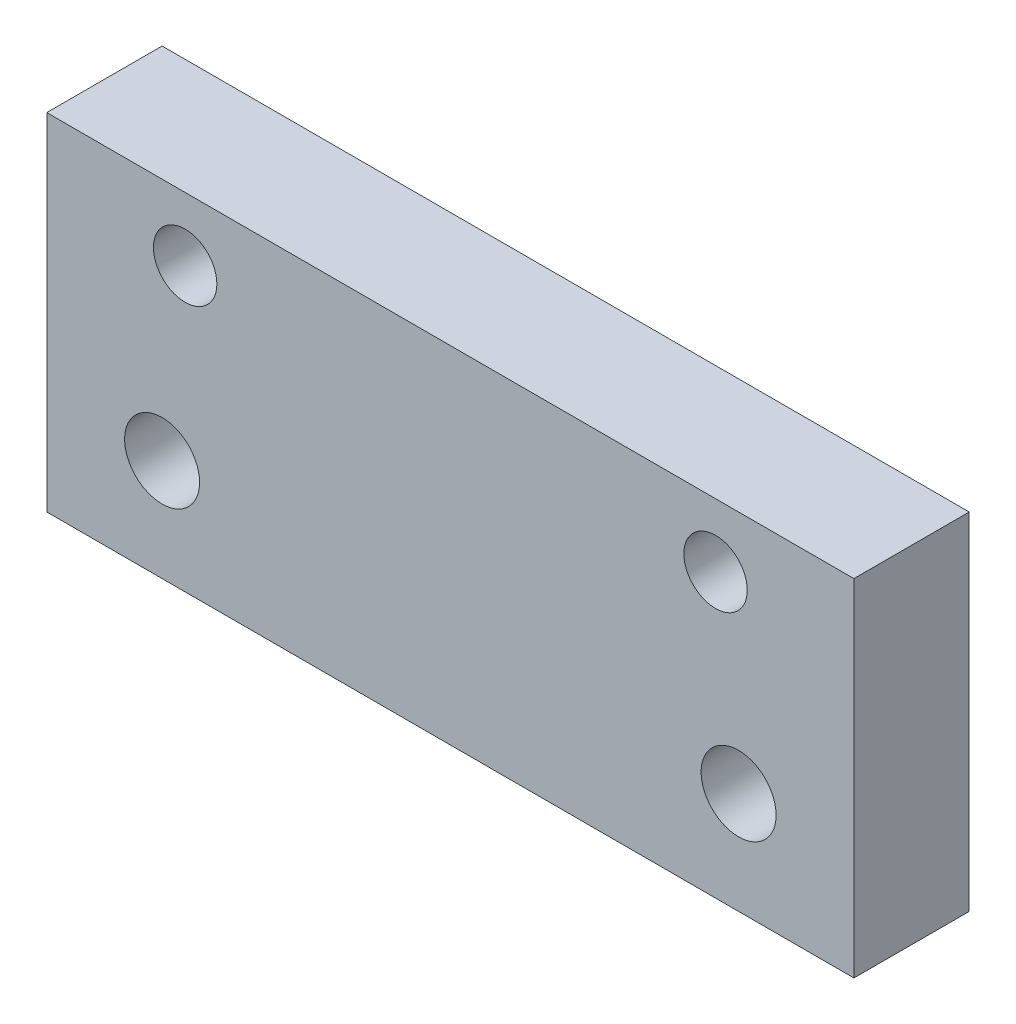
SolidWorks part; units mm, degrees
ref_plane "Front Plane" through (0, 0, 0) normal (0, 0, 1) x (1, 0, 0)
ref_plane "Top Plane" through (0, 0, 0) normal (0, 1, 0) x (1, 0, 0)
ref_plane "Right Plane" through (0, 0, 0) normal (1, 0, 0) x (0, 0, -1)
sketch "Sketch1" plane through (0, 0, 0) normal (0, 0, 1) x (1, 0, 0)
  line L1 (-35, 15) -> (35, 15)
  line L2 (-35, 15) -> (-35, -15)
  line L3 (-35, -15) -> (35, -15)
  line L4 (35, 15) -> (35, -15)
  line L5 (-35, 15) -> (35, -15) construction
  line L6 (-35, -15) -> (35, 15) construction
  circle A0 centre (-25, -6.1504) radius 3.25
  circle A1 centre (25, -6.1504) radius 3.25
  circle A2 centre (-23, 9.5) radius 2.75
  circle A3 centre (23, 9.5) radius 2.75
  point P0 (0, 0)
  point P14 (0, 0)
  point P15 (0, 0)
  point P17 (0, 0)
  dimension "D3" = 6.5
  dimension "D4" = 6.5
  dimension "D7" = 5.5
  dimension "D1" = 70
  dimension "D2" = 30
  dimension "D5" = 10
  dimension "D6" = 10
  dimension "D8" = 12
  dimension "D9" = 58
  dimension "D10" = 5.5
extrude "Boss-Extrude1" add sketch "Sketch1" along normal blind 10
sketch "Sketch3" plane through (0, 0, 0) normal (0, 0, -1) x (-1, 0, 0)
  circle A0 centre (-23, 9.5) radius 5
  circle A1 centre (23, 9.5) radius 5
  dimension "D1" = 10
extrude "Cut-Extrude1" cut sketch "Sketch3" against normal blind 5.4
